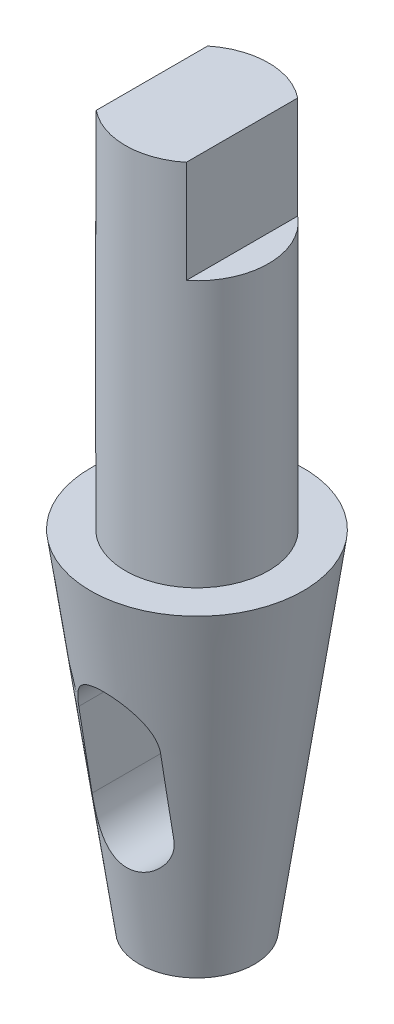
SolidWorks part; units mm, degrees
material "Сталь"
ref_plane "Спереди" through (0, 0, 0) normal (0, 0, 1) x (1, 0, 0)
ref_plane "Сверху" through (0, 0, 0) normal (0, 1, 0) x (1, 0, 0)
ref_plane "Справа" through (0, 0, 0) normal (1, 0, 0) x (0, 0, -1)
sketch "Эскиз1" plane through (0, 0, 0) normal (0, 0, 1) x (1, 0, 0)
  line L0 (0, 0) -> (0, -194.008) construction
  line L1 (0, 0) -> (17.5, 0)
  line L2 (17.5, 0) -> (17.5, -90)
  line L3 (17.5, -90) -> (26, -90)
  line L4 (26, -90) -> (14.054, -175)
  line L5 (14.054, -175) -> (0, -175)
  line L6 (0, 0) -> (0, -175)
  dimension "D1" = 35
  dimension "D2" = 175
  dimension "D3" = 52
  dimension "D4" = 8
  dimension "D5" = 90
revolve "Повернуть1" add sketch "Эскиз1" angle 360 about L0
sketch "Эскиз2" plane through (0, 0, 0) normal (0, 0, 1) x (1, 0, 0)
  line L0 (0, 0) -> (0, -175) construction
  line L1 (17.5, 0) -> (-17.5, 0) construction
  line L2 (-14.054, -175) -> (14.054, -175) construction
  line L3 (0, -123) -> (0, -143) construction
  line L4 (10, -123) -> (10, -143)
  line L5 (-10, -123) -> (-10, -143)
  line L7 (26, -90) -> (-26, -90) construction
  arc A0 (10, -123) -> (-10, -123) centre (0, -123) ccw
  arc A1 (-10, -143) -> (10, -143) centre (0, -143) ccw
  point P8 (0, -133)
  dimension "D2" = 40
  dimension "D3" = 23
  dimension "D1" = 20
extrude "Вырез-Вытянуть1" cut sketch "Эскиз2" against normal mid plane 50
sketch "Эскиз3" plane through (0, 0, 0) normal (0, 1, 0) x (1, 0, 0)
  line L0 (-11, 13.6107) -> (-11, -13.6107)
  line L1 (11, 13.6107) -> (11, -13.6107)
  circle A1 centre (0, 0) radius 17.5
  circle A2 centre (0, 0) radius 17.5
  circle M2 centre (0, 0) radius 17.5
  dimension "D2" = 11
  dimension "D1" = 0
extrude "Вырез-Вытянуть2" cut sketch "Эскиз3" against normal blind 25 contours L0 M2 | L1 M2
